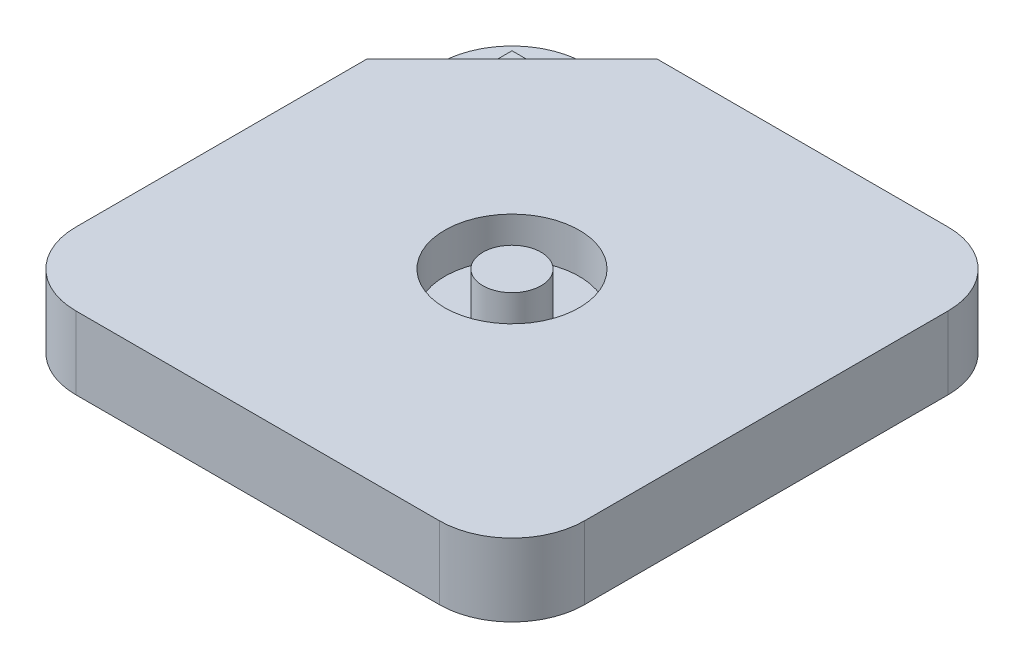
SolidWorks part; units mm, degrees
ref_plane "前视基准面" through (0, 0, 0) normal (0, 0, 1) x (1, 0, 0)
ref_plane "上视基准面" through (0, 0, 0) normal (0, 1, 0) x (1, 0, 0)
ref_plane "右视基准面" through (0, 0, 0) normal (1, 0, 0) x (0, 0, -1)
sketch "草图1" plane through (0, 0, 0) normal (0, 1, 0) x (1, 0, 0)
  line L1 (-35, 35) -> (35, 35)
  line L2 (-35, 35) -> (-35, -35)
  line L3 (-35, -35) -> (35, -35)
  line L4 (35, 35) -> (35, -35)
  line L5 (-35, 35) -> (35, -35) construction
  line L6 (-35, -35) -> (35, 35) construction
  point P0 (0, 0)
  dimension "D1" = 70
  dimension "D2" = 70
extrude "凸台-拉伸1" add sketch "草图1" along normal blind 10
sketch "草图2" plane through (0, 10, 0) normal (0, 1, 0) x (1, 0, 0)
  circle A0 centre (0, 0) radius 9.25
  dimension "D1" = 18.5
extrude "切除-拉伸1" cut sketch "草图2" against normal blind 5.5
sketch "草图3" plane through (0, 4.5, 0) normal (0, 1, 0) x (1, 0, 0)
  circle A0 centre (0, 0) radius 4
  dimension "D1" = 8
extrude "凸台-拉伸2" add sketch "草图3" along normal blind 5.5
sketch "草图4" plane through (0, 10, 0) normal (0, 1, 0) x (1, 0, 0)
  line L0 (-35, 35) -> (-15, 35)
  line L1 (35, 35) -> (-35, 35) construction
  line L2 (-15, 35) -> (-35, 15)
  line L3 (-35, 35) -> (-35, -35) construction
  line L4 (-35, 15) -> (-35, 35)
  dimension "D1" = 20
  dimension "D2" = 20
extrude "切除-拉伸2" cut sketch "草图4" against normal blind 5.5
sketch "草图5" plane through (0, 4.5, 0) normal (0, 1, 0) x (1, 0, 0)
  line L0 (-23, 27) -> (-27, 27)
  line L1 (-35, 15) -> (-15, 35) construction
  line L2 (-27, 27) -> (-27, 23)
  line L3 (-27, 23) -> (-23, 27)
  point P4 (-25, 25)
  point P6 (-25, 25)
  dimension "D1" = 4
extrude "凸台-拉伸3" add sketch "草图5" along normal blind 4.5
fillet "圆角1" radius 10 4 edges at (-35, 5, 35) (35, 5, 35) (35, 5, -35) (-35, 2.25, -35)
